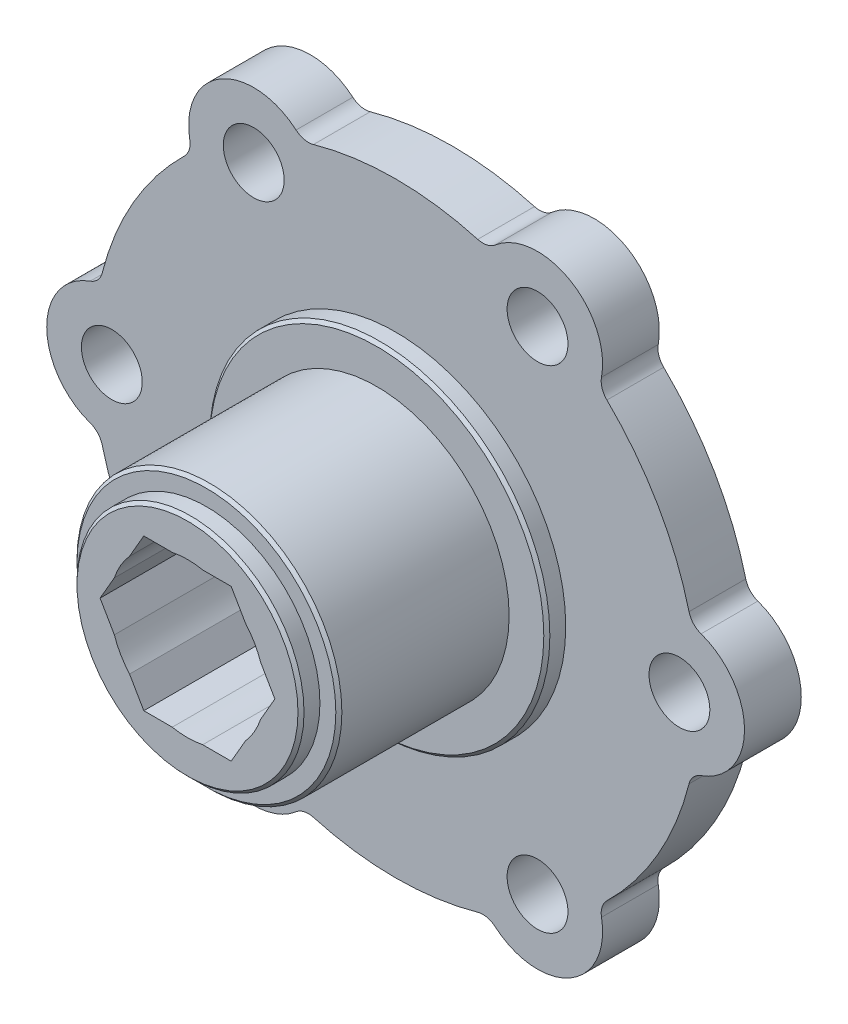
SolidWorks part; units mm, degrees
material "2024-O"
ref_plane "Front Plane" through (0, 0, 0) normal (0, 0, 1) x (1, 0, 0)
ref_plane "Top Plane" through (0, 0, 0) normal (0, 1, 0) x (1, 0, 0)
ref_plane "Right Plane" through (0, 0, 0) normal (1, 0, 0) x (0, 0, -1)
sketch "Sketch1" plane through (0, 0, 0) normal (0, 0, 1) x (1, 0, 0)
  arc A0 (4.4468, 31.4492) -> (4.4468, 20.7172) centre (5.461, 26.0832) ccw
  arc A1 (4.4468, 20.7172) -> (4.4468, 31.4492) centre (29.2735, 26.0832) ccw
extrude "Boss-Extrude1" add sketch "Sketch1" against normal blind 4.7625
sketch "Sketch2" plane through (0, 0, 0) normal (0, 0, 1) x (1, 0, 0)
  arc A0 (21.5072, 1.8997) -> (12.2131, 7.2657) centre (29.2735, 26.0832) cw
  arc A1 (12.2131, 7.2657) -> (21.5072, 1.8997) centre (17.3672, 5.461) ccw
extrude "Boss-Extrude2" add sketch "Sketch2" against normal blind 4.7625
sketch "Sketch3" plane through (0, 0, 0) normal (0, 0, 1) x (1, 0, 0)
  arc A0 (46.3339, 7.2657) -> (37.0398, 1.8997) centre (29.2735, 26.0832) cw
  arc A1 (37.0398, 1.8997) -> (46.3339, 7.2657) centre (41.1797, 5.461) ccw
extrude "Boss-Extrude3" add sketch "Sketch3" against normal blind 4.7625
sketch "Sketch4" plane through (0, 0, 0) normal (0, 0, 1) x (1, 0, 0)
  arc A0 (54.1002, 31.4492) -> (54.1002, 20.7172) centre (29.2735, 26.0832) cw
  arc A1 (54.1002, 20.7172) -> (54.1002, 31.4492) centre (53.086, 26.0832) ccw
extrude "Boss-Extrude4" add sketch "Sketch4" against normal blind 4.7625
sketch "Sketch5" plane through (0, 0, 0) normal (0, 0, 1) x (1, 0, 0)
  arc A0 (37.0398, 50.2668) -> (46.3339, 44.9008) centre (29.2735, 26.0832) cw
  arc A1 (46.3339, 44.9008) -> (37.0398, 50.2668) centre (41.1798, 46.7055) ccw
extrude "Boss-Extrude5" add sketch "Sketch5" against normal blind 4.7625
ref_plane "Plane1" through (0, 0, -4.7625) normal (0, 0, -1) x (-1, 0, 0)
sketch "Sketch6" plane through (0, 0, -4.7625) normal (0, 0, -1) x (-1, 0, 0)
  arc A0 (-12.2131, 44.9008) -> (-21.5072, 50.2668) centre (-17.3673, 46.7055) ccw
  arc A1 (-21.5072, 50.2668) -> (-12.2131, 44.9008) centre (-29.2735, 26.0832) cw
extrude "Boss-Extrude6" add sketch "Sketch6" against normal blind 4.7625
sketch "Sketch7" plane through (0, 0, 0) normal (0, 0, 1) x (1, 0, 0)
  circle A0 centre (29.2735, 26.0832) radius 14.2748
extrude "Boss-Extrude7" add sketch "Sketch7" along normal blind 1.5875
sketch "Sketch8" plane through (0, 0, 1.5875) normal (0, 0, 1) x (1, 0, 0)
  circle A0 centre (29.2735, 26.0832) radius 11.1125
extrude "Boss-Extrude8" add sketch "Sketch8" along normal blind 14.2875
sketch "Sketch9" plane through (0, 0, 15.875) normal (0, 0, 1) x (1, 0, 0)
  circle A0 centre (29.2735, 26.0832) radius 9.525
extrude "Boss-Extrude9" add sketch "Sketch9" along normal blind 1.5875
sketch "Sketch10" plane through (0, 0, -4.7625) normal (0, 0, -1) x (-1, 0, 0)
  circle A0 centre (-29.2735, 26.0832) radius 14.2748
extrude "Boss-Extrude10" add sketch "Sketch10" along normal blind 1.5875
sketch "Sketch11" plane through (0, 0, -6.35) normal (0, 0, -1) x (-1, 0, 0)
  circle A0 centre (-29.2735, 26.0832) radius 9.525
extrude "Boss-Extrude11" add sketch "Sketch11" along normal blind 1.5875
sketch "Sketch12" plane through (0, 0, -7.9375) normal (0, 0, -1) x (-1, 0, 0)
  line L0 (-24.4124, 30.3636) -> (-25.6073, 32.4332)
  line L1 (-25.6073, 32.4332) -> (-27.9972, 32.4332)
  line L2 (-30.5498, 32.4332) -> (-32.9397, 32.4332)
  line L3 (-32.9397, 32.4332) -> (-34.1346, 30.3636)
  line L4 (-35.4109, 28.1529) -> (-36.6058, 26.0832)
  line L5 (-36.6058, 26.0832) -> (-35.4109, 24.0136)
  line L6 (-34.1346, 21.8029) -> (-32.9397, 19.7332)
  line L7 (-32.9397, 19.7332) -> (-30.5498, 19.7332)
  line L8 (-27.9972, 19.7332) -> (-25.6073, 19.7332)
  line L9 (-25.6073, 19.7332) -> (-24.4124, 21.8029)
  line L10 (-23.1361, 24.0136) -> (-21.9412, 26.0832)
  line L11 (-21.9412, 26.0832) -> (-23.1361, 28.1529)
  arc A0 (-27.9972, 32.4332) -> (-30.5498, 32.4332) centre (-29.2735, 26.0832) ccw
  arc A1 (-34.1346, 30.3636) -> (-35.4109, 28.1529) centre (-29.2735, 26.0832) ccw
  arc A2 (-35.4109, 24.0136) -> (-34.1346, 21.8029) centre (-29.2735, 26.0832) ccw
  arc A3 (-30.5498, 19.7332) -> (-27.9972, 19.7332) centre (-29.2735, 26.0832) ccw
  arc A4 (-24.4124, 21.8029) -> (-23.1361, 24.0136) centre (-29.2735, 26.0832) ccw
  arc A5 (-23.1361, 28.1529) -> (-24.4124, 30.3636) centre (-29.2735, 26.0832) ccw
extrude "Cut-Extrude1" cut sketch "Sketch12" against normal through all
hole_wizard "#7 (0.201) Diameter Hole1" positions "Sketch14" profile "Sketch13" hole size "#7" standard "ANSI Inch"
sketch "Sketch14" plane through (0, 0, 0) normal (0, 0, 1) x (1, 0, 0)
  point P0 (41.1798, 46.7055)
  point P1 (53.086, 26.0832)
  point P2 (41.1797, 5.461)
  point P3 (17.3672, 5.461)
  point P4 (5.461, 26.0832)
sketch "Sketch13" plane through (41.1798, 46.7055, 0) normal (1, 0, 0) x (0, -1, 0)
  line L0 (0, 0) -> (0, 7.9375)
  line L1 (0, 7.9375) -> (2.5527, 7.9375)
  line L2 (2.5527, 7.9375) -> (2.5527, 0)
  line L5 (2.5527, 0) -> (0, 0)
  line L11 (0, -6.35) -> (0, 107.95) construction
  dimension "Thru Hole Dia." = 5.1054
  dimension "Thru Hole Depth" = 7.9375
hole_wizard "#7 (0.201) Diameter Hole2" positions "Sketch16" profile "Sketch15" hole size "#7" standard "ANSI Inch"
sketch "Sketch16" plane through (0, 0, -4.7625) normal (0, 0, -1) x (-1, 0, 0)
  point P0 (-17.3673, 46.7055)
sketch "Sketch15" plane through (17.3673, 46.7055, -4.7625) normal (1, 0, 0) x (0, 1, 0)
  line L0 (0, 0) -> (0, 22.225)
  line L1 (0, 22.225) -> (2.5527, 22.225)
  line L2 (2.5527, 22.225) -> (2.5527, 0)
  line L5 (2.5527, 0) -> (0, 0)
  line L11 (0, -6.35) -> (0, 107.95) construction
  dimension "Thru Hole Dia." = 5.1054
  dimension "Thru Hole Depth" = 22.225
chamfer "Chamfer1" distance 0.254 angle 45 5 edges at (40.386, 26.0832, 15.875) (43.5483, 26.0832, 1.5875) (19.7485, 26.0832, -7.9375) (38.7985, 26.0832, 17.4625) (14.9987, 26.0832, -6.35)
fillet "Fillet1" radius 1.5875 12 edges at (54.1002, 20.7172, -2.3812) (54.1002, 31.4492, -2.3812) (12.2131, 44.9008, -2.3812) (21.5072, 50.2668, -2.3812) (46.3339, 44.9008, -2.3812) (37.0398, 50.2668, -2.3812) (4.4468, 31.4492, -2.3812) (4.4468, 20.7172, -2.3812) (12.2131, 7.2657, -2.3812) (21.5072, 1.8997, -2.3812) (37.0398, 1.8997, -2.3812) (46.3339, 7.2657, -2.3812)
